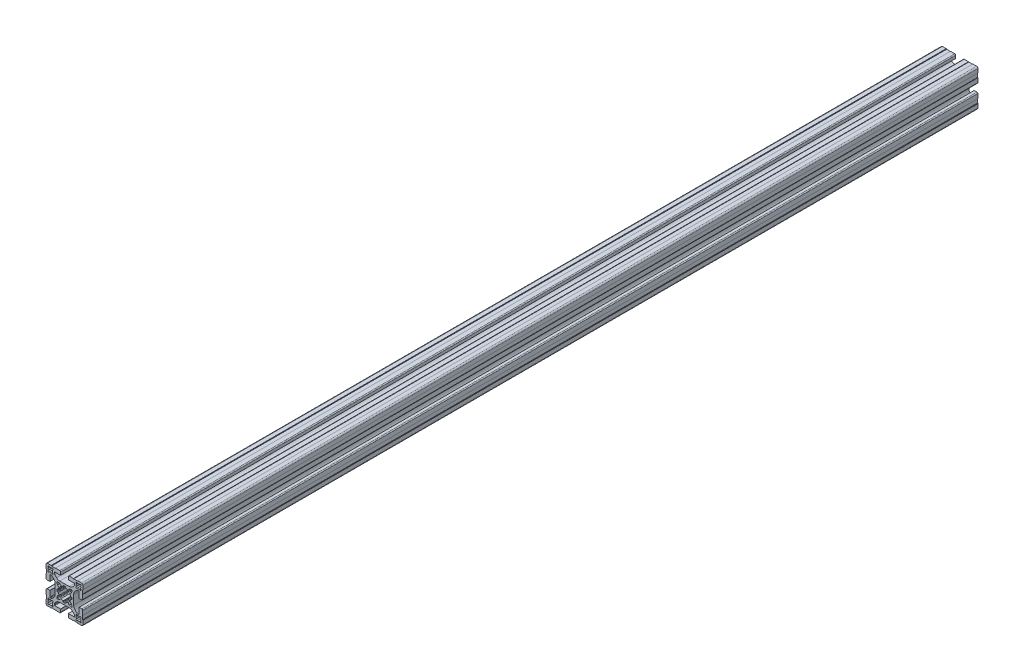
SolidWorks part; units mm, degrees
ref_plane "Plano frontal" through (0, 0, 0) normal (0, 0, 1) x (1, 0, 0)
ref_plane "Plano superior" through (0, 0, 0) normal (0, 1, 0) x (1, 0, 0)
ref_plane "Plano direito" through (0, 0, 0) normal (1, 0, 0) x (0, 0, -1)
sketch "Esboço1" plane through (0, 0, 0) normal (0, 0, 1) x (1, 0, 0)
  line B0 (-17.8572, 16.7966) -> (-17.4167, 16.356)
  arc B1 (-16.7966, 17.8572) -> (-17.8572, 16.7966) centre (-17.3269, 17.3269) ccw
  line B2 (-16.356, 17.4167) -> (-16.7966, 17.8572)
  arc B3 (-14.044, 17.4167) -> (-16.356, 17.4167) centre (-15.2, 15.2) ccw
  line B4 (-13.6034, 17.8572) -> (-14.044, 17.4167)
  arc B5 (-12.5428, 16.7966) -> (-13.6034, 17.8572) centre (-13.0731, 17.3269) ccw
  line B6 (-12.9833, 16.356) -> (-12.5428, 16.7966)
  arc B7 (-12.9833, 14.044) -> (-12.9833, 16.356) centre (-15.2, 15.2) ccw
  line B8 (-12.5428, 13.6034) -> (-12.9833, 14.044)
  arc B9 (-13.6034, 12.5428) -> (-12.5428, 13.6034) centre (-13.0731, 13.0731) ccw
  line B10 (-14.044, 12.9833) -> (-13.6034, 12.5428)
  arc B11 (-16.356, 12.9833) -> (-14.044, 12.9833) centre (-15.2, 15.2) ccw
  line B12 (-16.7966, 12.5428) -> (-16.356, 12.9833)
  arc B13 (-17.8572, 13.6034) -> (-16.7966, 12.5428) centre (-17.3269, 13.0731) ccw
  line B14 (-17.4167, 14.044) -> (-17.8572, 13.6034)
  arc B15 (-17.4167, 16.356) -> (-17.4167, 14.044) centre (-15.2, 15.2) ccw
  line B16 (17.4167, 14.044) -> (17.8572, 13.6034)
  arc B17 (16.7966, 12.5428) -> (17.8572, 13.6034) centre (17.3269, 13.0731) ccw
  line B18 (16.7966, 12.5428) -> (16.356, 12.9833)
  arc B19 (14.044, 12.9833) -> (16.356, 12.9833) centre (15.2, 15.2) ccw
  line B20 (14.044, 12.9833) -> (13.6034, 12.5428)
  arc B21 (12.5428, 13.6034) -> (13.6034, 12.5428) centre (13.0731, 13.0731) ccw
  line B22 (12.5428, 13.6034) -> (12.9833, 14.044)
  arc B23 (12.9833, 16.356) -> (12.9833, 14.044) centre (15.2, 15.2) ccw
  line B24 (12.9833, 16.356) -> (12.5428, 16.7966)
  arc B25 (13.6034, 17.8572) -> (12.5428, 16.7966) centre (13.0731, 17.3269) ccw
  line B26 (13.6034, 17.8572) -> (14.044, 17.4167)
  arc B27 (16.356, 17.4167) -> (14.044, 17.4167) centre (15.2, 15.2) ccw
  line B28 (16.356, 17.4167) -> (16.7966, 17.8572)
  arc B29 (17.8572, 16.7966) -> (16.7966, 17.8572) centre (17.3269, 17.3269) ccw
  line B30 (17.8572, 16.7966) -> (17.4167, 16.356)
  arc B31 (17.4167, 14.044) -> (17.4167, 16.356) centre (15.2, 15.2) ccw
  line B32 (-17.4167, -14.044) -> (-17.8572, -13.6034)
  arc B33 (-16.7966, -12.5428) -> (-17.8572, -13.6034) centre (-17.3269, -13.0731) ccw
  line B34 (-16.7966, -12.5428) -> (-16.356, -12.9833)
  arc B35 (-14.044, -12.9833) -> (-16.356, -12.9833) centre (-15.2, -15.2) ccw
  line B36 (-14.044, -12.9833) -> (-13.6034, -12.5428)
  arc B37 (-12.5428, -13.6034) -> (-13.6034, -12.5428) centre (-13.0731, -13.0731) ccw
  line B38 (-12.5428, -13.6034) -> (-12.9833, -14.044)
  arc B39 (-12.9833, -16.356) -> (-12.9833, -14.044) centre (-15.2, -15.2) ccw
  line B40 (-12.9833, -16.356) -> (-12.5428, -16.7966)
  arc B41 (-13.6034, -17.8572) -> (-12.5428, -16.7966) centre (-13.0731, -17.3269) ccw
  line B42 (-13.6034, -17.8572) -> (-14.044, -17.4167)
  arc B43 (-16.356, -17.4167) -> (-14.044, -17.4167) centre (-15.2, -15.2) ccw
  line B44 (-16.356, -17.4167) -> (-16.7966, -17.8572)
  arc B45 (-17.8572, -16.7966) -> (-16.7966, -17.8572) centre (-17.3269, -17.3269) ccw
  line B46 (-17.8572, -16.7966) -> (-17.4167, -16.356)
  arc B47 (-17.4167, -14.044) -> (-17.4167, -16.356) centre (-15.2, -15.2) ccw
  line B48 (17.8572, -16.7966) -> (17.4167, -16.356)
  arc B49 (16.7966, -17.8572) -> (17.8572, -16.7966) centre (17.3269, -17.3269) ccw
  line B50 (16.356, -17.4167) -> (16.7966, -17.8572)
  arc B51 (14.044, -17.4167) -> (16.356, -17.4167) centre (15.2, -15.2) ccw
  line B52 (13.6034, -17.8572) -> (14.044, -17.4167)
  arc B53 (12.5428, -16.7966) -> (13.6034, -17.8572) centre (13.0731, -17.3269) ccw
  line B54 (12.9833, -16.356) -> (12.5428, -16.7966)
  arc B55 (12.9833, -14.044) -> (12.9833, -16.356) centre (15.2, -15.2) ccw
  line B56 (12.5428, -13.6034) -> (12.9833, -14.044)
  arc B57 (13.6034, -12.5428) -> (12.5428, -13.6034) centre (13.0731, -13.0731) ccw
  line B58 (14.044, -12.9833) -> (13.6034, -12.5428)
  arc B59 (16.356, -12.9833) -> (14.044, -12.9833) centre (15.2, -15.2) ccw
  line B60 (16.7966, -12.5428) -> (16.356, -12.9833)
  arc B61 (17.8572, -13.6034) -> (16.7966, -12.5428) centre (17.3269, -13.0731) ccw
  line B62 (17.4167, -14.044) -> (17.8572, -13.6034)
  arc B63 (17.4167, -16.356) -> (17.4167, -14.044) centre (15.2, -15.2) ccw
  line B64 (4.15, -18.8) -> (4.15, -15.9)
  arc B65 (4.25, -15.8) -> (4.15, -15.9) centre (4.25, -15.9) ccw
  line B66 (4.25, -15.8) -> (10.5, -15.8)
  arc B67 (10.5, -15.8) -> (11, -15.3) centre (10.5, -15.3) ccw
  line B68 (11, -15.3) -> (11, -14.4497)
  arc B69 (11, -14.4497) -> (10.5607, -13.3891) centre (9.5, -14.4497) ccw
  line B70 (10.5607, -13.3891) -> (8.636, -11.4645)
  arc B71 (8.636, -11.4645) -> (5.1005, -10) centre (5.1005, -15) ccw
  line B72 (5.1005, -10) -> (0, -10)
  line B73 (0, -10) -> (-5.1005, -10)
  arc B74 (-5.1005, -10) -> (-8.636, -11.4645) centre (-5.1005, -15) ccw
  line B75 (-8.636, -11.4645) -> (-10.5607, -13.3891)
  arc B76 (-10.5607, -13.3891) -> (-11, -14.4497) centre (-9.5, -14.4497) ccw
  line B77 (-11, -14.4497) -> (-11, -15.3)
  arc B78 (-11, -15.3) -> (-10.5, -15.8) centre (-10.5, -15.3) ccw
  line B79 (-10.5, -15.8) -> (-4.25, -15.8)
  arc B80 (-4.15, -15.9) -> (-4.25, -15.8) centre (-4.25, -15.9) ccw
  line B81 (-4.15, -15.9) -> (-4.15, -18.8)
  arc B82 (-5.15, -19.8) -> (-4.15, -18.8) centre (-5.15, -18.8) ccw
  line B83 (-5.15, -19.8) -> (-9.8, -19.8)
  line B84 (-9.8, -19.8) -> (-10, -19.6)
  line B85 (-10, -19.6) -> (-14, -19.6)
  line B86 (-14, -19.6) -> (-14.4, -20)
  line B87 (-14.4, -20) -> (-18.5, -20)
  arc B88 (-20, -18.5) -> (-18.5, -20) centre (-18.5, -18.5) ccw
  line B89 (-20, -18.5) -> (-20, -14.4)
  line B90 (-20, -14.4) -> (-19.6, -14)
  line B91 (-19.6, -14) -> (-19.6, -10)
  line B92 (-19.6, -10) -> (-19.8, -9.8)
  line B93 (-19.8, -9.8) -> (-19.8, -5.15)
  arc B94 (-18.8, -4.15) -> (-19.8, -5.15) centre (-18.8, -5.15) ccw
  line B95 (-18.8, -4.15) -> (-15.9, -4.15)
  arc B96 (-15.8, -4.25) -> (-15.9, -4.15) centre (-15.9, -4.25) ccw
  line B97 (-15.8, -4.25) -> (-15.8, -10.5)
  arc B98 (-15.8, -10.5) -> (-15.3, -11) centre (-15.3, -10.5) ccw
  line B99 (-15.3, -11) -> (-14.4497, -11)
  arc B100 (-14.4497, -11) -> (-13.3891, -10.5607) centre (-14.4497, -9.5) ccw
  line B101 (-13.3891, -10.5607) -> (-11.4645, -8.636)
  arc B102 (-11.4645, -8.636) -> (-10, -5.1005) centre (-15, -5.1005) ccw
  line B103 (-10, -5.1005) -> (-10, 0)
  line B104 (-10, 0) -> (-10, 5.1005)
  arc B105 (-10, 5.1005) -> (-11.4645, 8.636) centre (-15, 5.1005) ccw
  line B106 (-11.4645, 8.636) -> (-13.3891, 10.5607)
  arc B107 (-13.3891, 10.5607) -> (-14.4497, 11) centre (-14.4497, 9.5) ccw
  line B108 (-14.4497, 11) -> (-15.3, 11)
  arc B109 (-15.3, 11) -> (-15.8, 10.5) centre (-15.3, 10.5) ccw
  line B110 (-15.8, 10.5) -> (-15.8, 4.25)
  arc B111 (-15.9, 4.15) -> (-15.8, 4.25) centre (-15.9, 4.25) ccw
  line B112 (-15.9, 4.15) -> (-18.8, 4.15)
  arc B113 (-19.8, 5.15) -> (-18.8, 4.15) centre (-18.8, 5.15) ccw
  line B114 (-19.8, 5.15) -> (-19.8, 9.8)
  line B115 (-19.8, 9.8) -> (-19.6, 10)
  line B116 (-19.6, 10) -> (-19.6, 14)
  line B117 (-19.6, 14) -> (-20, 14.4)
  line B118 (-20, 14.4) -> (-20, 18.5)
  arc B119 (-18.5, 20) -> (-20, 18.5) centre (-18.5, 18.5) ccw
  line B120 (-18.5, 20) -> (-14.4, 20)
  line B121 (-14.4, 20) -> (-14, 19.6)
  line B122 (-14, 19.6) -> (-10, 19.6)
  line B123 (-10, 19.6) -> (-9.8, 19.8)
  line B124 (-9.8, 19.8) -> (-5.15, 19.8)
  arc B125 (-4.15, 18.8) -> (-5.15, 19.8) centre (-5.15, 18.8) ccw
  line B126 (-4.15, 18.8) -> (-4.15, 15.9)
  arc B127 (-4.25, 15.8) -> (-4.15, 15.9) centre (-4.25, 15.9) ccw
  line B128 (-4.25, 15.8) -> (-10.5, 15.8)
  arc B129 (-10.5, 15.8) -> (-11, 15.3) centre (-10.5, 15.3) ccw
  line B130 (-11, 15.3) -> (-11, 14.4497)
  arc B131 (-11, 14.4497) -> (-10.5607, 13.3891) centre (-9.5, 14.4497) ccw
  line B132 (-10.5607, 13.3891) -> (-8.636, 11.4645)
  arc B133 (-8.636, 11.4645) -> (-5.1005, 10) centre (-5.1005, 15) ccw
  line B134 (-5.1005, 10) -> (0, 10)
  line B135 (0, 10) -> (5.1005, 10)
  arc B136 (5.1005, 10) -> (8.636, 11.4645) centre (5.1005, 15) ccw
  line B137 (8.636, 11.4645) -> (10.5607, 13.3891)
  arc B138 (10.5607, 13.3891) -> (11, 14.4497) centre (9.5, 14.4497) ccw
  line B139 (11, 14.4497) -> (11, 15.3)
  arc B140 (11, 15.3) -> (10.5, 15.8) centre (10.5, 15.3) ccw
  line B141 (10.5, 15.8) -> (4.25, 15.8)
  arc B142 (4.15, 15.9) -> (4.25, 15.8) centre (4.25, 15.9) ccw
  line B143 (4.15, 15.9) -> (4.15, 18.8)
  arc B144 (5.15, 19.8) -> (4.15, 18.8) centre (5.15, 18.8) ccw
  line B145 (5.15, 19.8) -> (9.8, 19.8)
  line B146 (9.8, 19.8) -> (10, 19.6)
  line B147 (10, 19.6) -> (14, 19.6)
  line B148 (14, 19.6) -> (14.4, 20)
  line B149 (14.4, 20) -> (18.5, 20)
  arc B150 (20, 18.5) -> (18.5, 20) centre (18.5, 18.5) ccw
  line B151 (20, 18.5) -> (20, 14.4)
  line B152 (20, 14.4) -> (19.6, 14)
  line B153 (19.6, 14) -> (19.6, 10)
  line B154 (19.6, 10) -> (19.8, 9.8)
  line B155 (19.8, 9.8) -> (19.8, 5.15)
  arc B156 (18.8, 4.15) -> (19.8, 5.15) centre (18.8, 5.15) ccw
  line B157 (18.8, 4.15) -> (15.9, 4.15)
  arc B158 (15.8, 4.25) -> (15.9, 4.15) centre (15.9, 4.25) ccw
  line B159 (15.8, 4.25) -> (15.8, 10.5)
  arc B160 (15.8, 10.5) -> (15.3, 11) centre (15.3, 10.5) ccw
  line B161 (15.3, 11) -> (14.4497, 11)
  arc B162 (14.4497, 11) -> (13.3891, 10.5607) centre (14.4497, 9.5) ccw
  line B163 (13.3891, 10.5607) -> (11.4645, 8.636)
  arc B164 (11.4645, 8.636) -> (10, 5.1005) centre (15, 5.1005) ccw
  line B165 (10, 5.1005) -> (10, 0)
  line B166 (10, 0) -> (10, -5.1005)
  arc B167 (10, -5.1005) -> (11.4645, -8.636) centre (15, -5.1005) ccw
  line B168 (11.4645, -8.636) -> (13.3891, -10.5607)
  arc B169 (13.3891, -10.5607) -> (14.4497, -11) centre (14.4497, -9.5) ccw
  line B170 (14.4497, -11) -> (15.3, -11)
  arc B171 (15.3, -11) -> (15.8, -10.5) centre (15.3, -10.5) ccw
  line B172 (15.8, -10.5) -> (15.8, -4.25)
  arc B173 (15.9, -4.15) -> (15.8, -4.25) centre (15.9, -4.25) ccw
  line B174 (15.9, -4.15) -> (18.8, -4.15)
  arc B175 (19.8, -5.15) -> (18.8, -4.15) centre (18.8, -5.15) ccw
  line B176 (19.8, -5.15) -> (19.8, -9.8)
  line B177 (19.8, -9.8) -> (19.6, -10)
  line B178 (19.6, -10) -> (19.6, -14)
  line B179 (19.6, -14) -> (20, -14.4)
  line B180 (20, -14.4) -> (20, -18.5)
  arc B181 (18.5, -20) -> (20, -18.5) centre (18.5, -18.5) ccw
  line B182 (18.5, -20) -> (14.4, -20)
  line B183 (14.4, -20) -> (14, -19.6)
  line B184 (14, -19.6) -> (10, -19.6)
  line B185 (10, -19.6) -> (9.8, -19.8)
  line B186 (9.8, -19.8) -> (5.15, -19.8)
  arc B187 (4.15, -18.8) -> (5.15, -19.8) centre (5.15, -18.8) ccw
  line B188 (-5.3139, -7.6355) -> (-7.6488, -8.2611)
  arc B189 (-8.2611, -7.6488) -> (-7.6488, -8.2611) centre (-7.7782, -7.7782) ccw
  line B190 (-8.2611, -7.6488) -> (-7.6355, -5.3139)
  arc B191 (-7.4569, -5.0466) -> (-7.6355, -5.3139) centre (-7.1525, -5.4433) ccw
  line B192 (-7.4569, -5.0466) -> (-5.744, -3.7322)
  arc B193 (-6.7007, -1.4225) -> (-5.744, -3.7322) centre (0, 0) ccw
  line B194 (-6.7007, -1.4225) -> (-7.5204, -1.3146)
  arc B195 (-7.9522, -0.8735) -> (-7.5204, -1.3146) centre (-7.4552, -0.8189) ccw
  arc B196 (-7.9522, 0.8735) -> (-7.9522, -0.8735) centre (0, 0) ccw
  arc B197 (-7.5204, 1.3146) -> (-7.9522, 0.8735) centre (-7.4552, 0.8189) ccw
  line B198 (-7.5204, 1.3146) -> (-6.7007, 1.4225)
  arc B199 (-5.744, 3.7322) -> (-6.7007, 1.4225) centre (0, 0) ccw
  line B200 (-5.744, 3.7322) -> (-7.4569, 5.0466)
  arc B201 (-7.6355, 5.3139) -> (-7.4569, 5.0466) centre (-7.1525, 5.4433) ccw
  line B202 (-7.6355, 5.3139) -> (-8.2611, 7.6488)
  arc B203 (-7.6488, 8.2611) -> (-8.2611, 7.6488) centre (-7.7782, 7.7782) ccw
  line B204 (-7.6488, 8.2611) -> (-5.3139, 7.6355)
  arc B205 (-5.0466, 7.4569) -> (-5.3139, 7.6355) centre (-5.4433, 7.1525) ccw
  line B206 (-5.0466, 7.4569) -> (-3.7322, 5.744)
  arc B207 (-1.4225, 6.7007) -> (-3.7322, 5.744) centre (0, 0) ccw
  line B208 (-1.4225, 6.7007) -> (-1.3146, 7.5204)
  arc B209 (-0.8735, 7.9522) -> (-1.3146, 7.5204) centre (-0.8189, 7.4552) ccw
  arc B210 (0.8735, 7.9522) -> (-0.8735, 7.9522) centre (0, 0) ccw
  arc B211 (1.3146, 7.5204) -> (0.8735, 7.9522) centre (0.8189, 7.4552) ccw
  line B212 (1.3146, 7.5204) -> (1.4225, 6.7007)
  arc B213 (3.7322, 5.744) -> (1.4225, 6.7007) centre (0, 0) ccw
  line B214 (3.7322, 5.744) -> (5.0466, 7.4569)
  arc B215 (5.3139, 7.6355) -> (5.0466, 7.4569) centre (5.4433, 7.1525) ccw
  line B216 (5.3139, 7.6355) -> (7.6488, 8.2611)
  arc B217 (8.2611, 7.6488) -> (7.6488, 8.2611) centre (7.7782, 7.7782) ccw
  line B218 (8.2611, 7.6488) -> (7.6355, 5.3139)
  arc B219 (7.4569, 5.0466) -> (7.6355, 5.3139) centre (7.1525, 5.4433) ccw
  line B220 (7.4569, 5.0466) -> (5.744, 3.7322)
  arc B221 (6.7007, 1.4225) -> (5.744, 3.7322) centre (0, 0) ccw
  line B222 (6.7007, 1.4225) -> (7.5204, 1.3146)
  arc B223 (7.9522, 0.8735) -> (7.5204, 1.3146) centre (7.4552, 0.8189) ccw
  arc B224 (7.9522, -0.8735) -> (7.9522, 0.8735) centre (0, 0) ccw
  arc B225 (7.5204, -1.3146) -> (7.9522, -0.8735) centre (7.4552, -0.8189) ccw
  line B226 (7.5204, -1.3146) -> (6.7007, -1.4225)
  arc B227 (5.744, -3.7322) -> (6.7007, -1.4225) centre (0, 0) ccw
  line B228 (5.744, -3.7322) -> (7.4569, -5.0466)
  arc B229 (7.6355, -5.3139) -> (7.4569, -5.0466) centre (7.1525, -5.4433) ccw
  line B230 (7.6355, -5.3139) -> (8.2611, -7.6488)
  arc B231 (7.6488, -8.2611) -> (8.2611, -7.6488) centre (7.7782, -7.7782) ccw
  line B232 (7.6488, -8.2611) -> (5.3139, -7.6355)
  arc B233 (5.0466, -7.4569) -> (5.3139, -7.6355) centre (5.4433, -7.1525) ccw
  line B234 (5.0466, -7.4569) -> (3.7322, -5.744)
  arc B235 (1.4225, -6.7007) -> (3.7322, -5.744) centre (0, 0) ccw
  line B236 (1.4225, -6.7007) -> (1.3146, -7.5204)
  arc B237 (0.8735, -7.9522) -> (1.3146, -7.5204) centre (0.8189, -7.4552) ccw
  arc B238 (-0.8735, -7.9522) -> (0.8735, -7.9522) centre (0, 0) ccw
  arc B239 (-1.3146, -7.5204) -> (-0.8735, -7.9522) centre (-0.8189, -7.4552) ccw
  line B240 (-1.3146, -7.5204) -> (-1.4225, -6.7007)
  arc B241 (-3.7322, -5.744) -> (-1.4225, -6.7007) centre (0, 0) ccw
  line B242 (-3.7322, -5.744) -> (-5.0466, -7.4569)
  arc B243 (-5.3139, -7.6355) -> (-5.0466, -7.4569) centre (-5.4433, -7.1525) ccw
sketch_block_instance "P40103-1"
sketch_block "P40103"
other "Item de detalhe3"
other "Item de detalhe4"
extrude "Ressalto-extrusão1" add sketch "Esboço1" along normal mid plane 970
